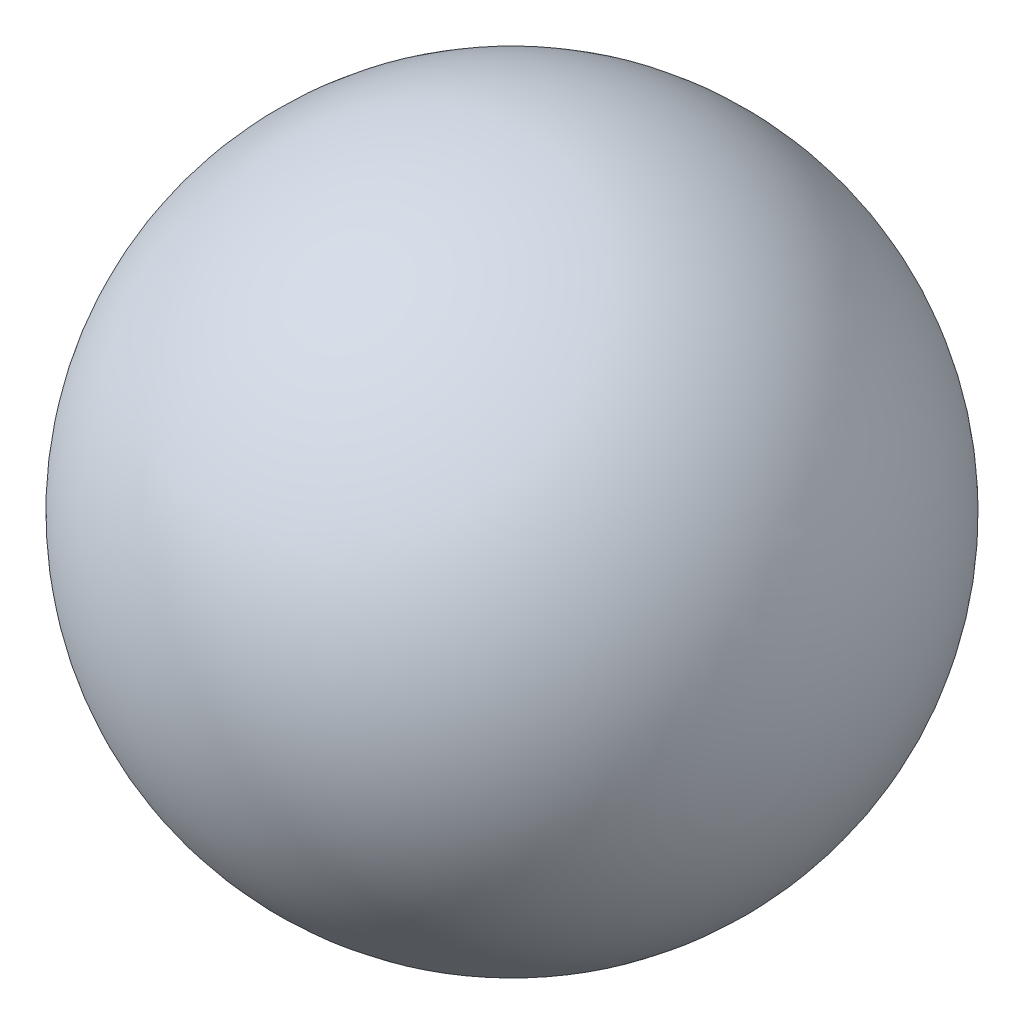
SolidWorks part; units mm, degrees
ref_plane "Front Plane" through (0, 0, 0) normal (0, 0, 1) x (1, 0, 0)
ref_plane "Top Plane" through (0, 0, 0) normal (0, 1, 0) x (1, 0, 0)
ref_plane "Right Plane" through (0, 0, 0) normal (1, 0, 0) x (0, 0, -1)
sketch "Sketch1" plane through (0, 0, 0) normal (0, 0, 1) x (1, 0, 0)
  line L0 (0, 12.7) -> (0, -12.7)
  arc A0 (0, 12.7) -> (0, -12.7) centre (0, 0) ccw
  dimension "D1" = 25.4
revolve "Revolve1" add sketch "Sketch1" angle 360 about L0
ref_plane "Plane1" through (0, -12.7, 0) normal (0, -1, 0) x (-1, 0, 0)
hole_wizard "1/4-20 Tapped Hole1" positions "Sketch4" profile "Sketch3" tap size "1/4-20" standard "ANSI Inch"
sketch "Sketch4" plane through (0, -12.7, 0) normal (0, -1, 0) x (-1, 0, 0)
  point P0 (0, 0)
sketch "Sketch3" plane through (0, -12.7, 0) normal (1, 0, 0) x (0, 0, -1)
  line L0 (0, 0) -> (0, 7.8838)
  line L1 (0, 7.8838) -> (2.5527, 6.35)
  line L2 (2.5527, 6.35) -> (2.5527, 0)
  line L5 (2.5527, 0) -> (0, 0)
  line L10 (0, 7.8838) -> (-2.5527, 6.35) construction
  line L11 (0, -6.35) -> (0, 107.95) construction
  dimension "Tap Drill Dia." = 5.1054
  dimension "Tap Drill Depth" = 6.35
  dimension "Drill Angle" = 118
cosmetic thread "Hole Thread1"
